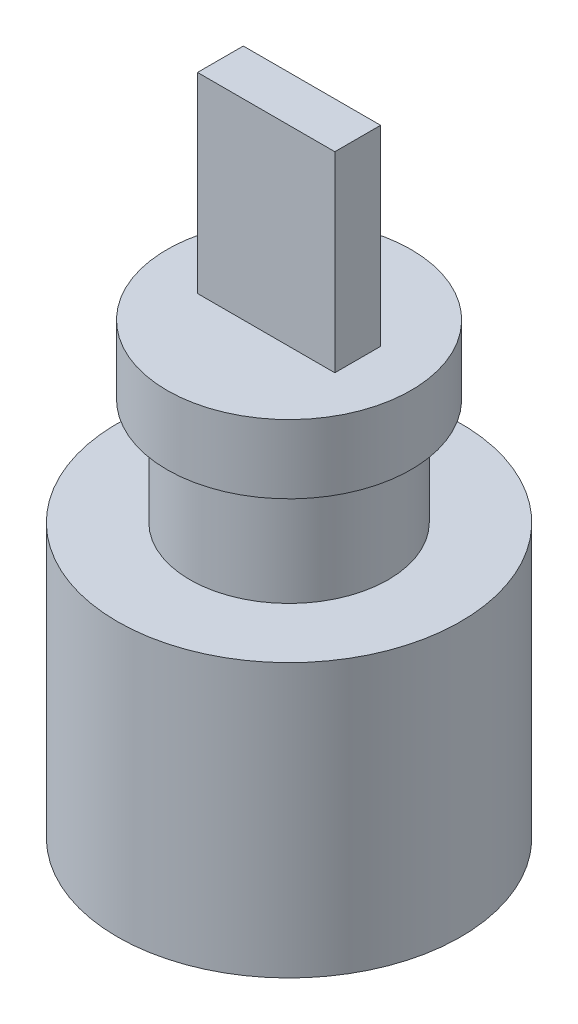
SolidWorks part; units mm, degrees
ref_plane "Piano frontale" through (0, 0, 0) normal (0, 0, 1) x (1, 0, 0)
ref_plane "Piano superiore" through (0, 0, 0) normal (0, 1, 0) x (1, 0, 0)
ref_plane "Piano destro" through (0, 0, 0) normal (1, 0, 0) x (0, 0, -1)
sketch "Schizzo1" plane through (0, 0, 0) normal (0, 1, 0) x (1, 0, 0)
  circle A0 centre (0, 0) radius 22.5
  dimension "D1" = 45
extrude "Estrusione-Estrusione1" add sketch "Schizzo1" along normal blind 35.8
sketch "Schizzo2" plane through (0, 35.8, 0) normal (0, 1, 0) x (1, 0, 0)
  circle A0 centre (0, 0) radius 13
  dimension "D1" = 26
extrude "Estrusione-Estrusione3" add sketch "Schizzo2" along normal blind 14 contours A0
sketch "Schizzo3" plane through (0, 49.8, 0) normal (0, 1, 0) x (1, 0, 0)
  circle A0 centre (0, 0) radius 16
  circle A1 centre (0, 0) radius 13
  circle A2 centre (0, 0) radius 13 construction
  dimension "D1" = 0
  dimension "D2" = 3
extrude "Estrusione-Estrusione4" add sketch "Schizzo3" along normal blind 9
sketch "Schizzo4" plane through (0, 58.8, 0) normal (0, 1, 0) x (1, 0, 0)
  line L1 (-9, 3) -> (9, 3)
  line L2 (-9, 3) -> (-9, -3)
  line L3 (-9, -3) -> (9, -3)
  line L4 (9, 3) -> (9, -3)
  line L5 (-9, 3) -> (9, -3) construction
  line L6 (-9, -3) -> (9, 3) construction
  point P0 (0, 0)
  dimension "D1" = 6
  dimension "D2" = 18
extrude "Estrusione-Estrusione5" add sketch "Schizzo4" along normal blind 25.1
